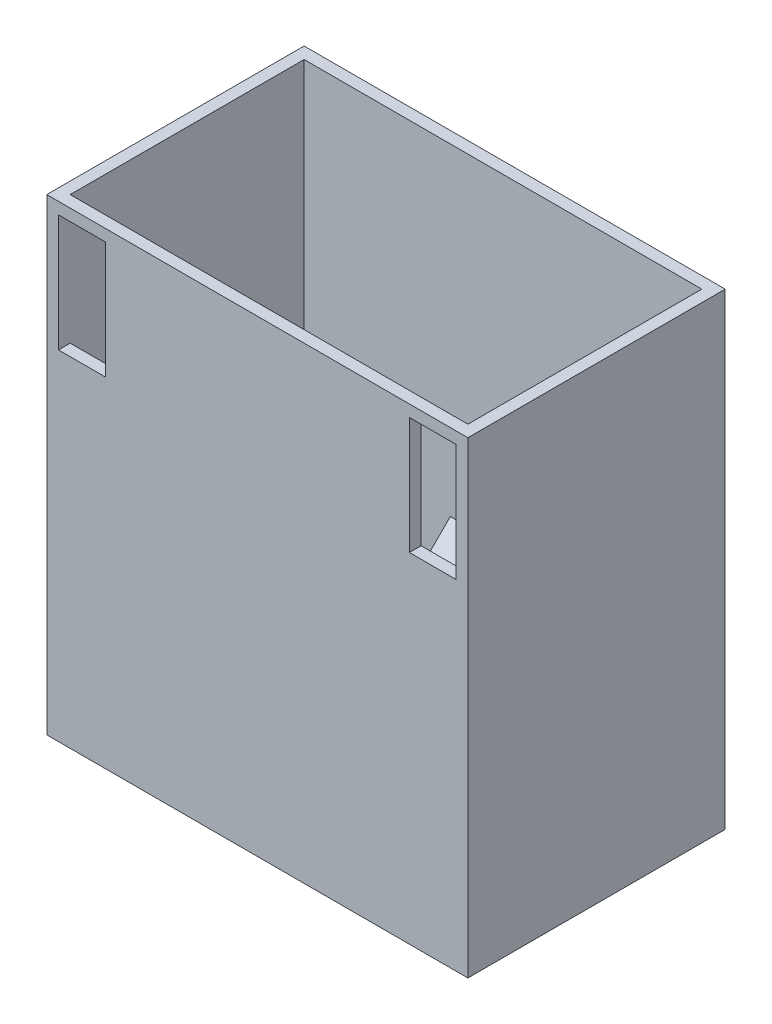
SolidWorks part; units mm, degrees
ref_plane "Front Plane" through (0, 0, 0) normal (0, 0, 1) x (1, 0, 0)
ref_plane "Top Plane" through (0, 0, 0) normal (0, 1, 0) x (1, 0, 0)
ref_plane "Right Plane" through (0, 0, 0) normal (1, 0, 0) x (0, 0, -1)
sketch "Sketch2" plane through (0, 0, 0) normal (0, 1, 0) x (1, 0, 0)
  line L1 (0, 0) -> (90, 0)
  line L2 (0, 0) -> (0, 55)
  line L3 (0, 55) -> (90, 55)
  line L4 (90, 0) -> (90, 55)
  dimension "D1" = 90
  dimension "D2" = 55
extrude "Boss-Extrude1" add sketch "Sketch2" along normal blind 100
sketch "Sketch3" plane through (0, 100, 0) normal (0, 1, 0) x (1, 0, 0)
  line L0 (2.5, 2.5) -> (2.5, 0) construction
  line L1 (2.5, 2.5) -> (87.5, 2.5)
  line L2 (2.5, 2.5) -> (2.5, 52.5)
  line L3 (2.5, 52.5) -> (87.5, 52.5)
  line L4 (87.5, 2.5) -> (87.5, 52.5)
  line L5 (0, 0) -> (90, 0) construction
  line L6 (2.5, 0) -> (2.5, 2.5) construction
  line L7 (0, 2.5) -> (2.5, 2.5) construction
  line L8 (0, 55) -> (0, 0) construction
  line L9 (87.5, 52.5) -> (87.5, 55) construction
  line L10 (90, 55) -> (0, 55) construction
  line L11 (87.5, 2.5) -> (90, 2.5) construction
  line L12 (90, 0) -> (90, 55) construction
  dimension "D1" = 2.5
extrude "Cut-Extrude1" cut sketch "Sketch3" against normal blind 95
ref_plane "Plane2" through (36.25, 0, 0) normal (1, 0, 0) x (0, 0, -1)
sketch "Sketch4" plane through (0, 0, 0) normal (0, -1, 0) x (1, 0, 0)
  line L0 (45, -55) -> (45, 0) construction
  line L1 (90, -55) -> (0, -55) construction
  line L2 (0, 0) -> (90, 0) construction
  line L4 (36.25, -25) -> (53.75, -25)
  line L5 (36.25, -25) -> (36.25, -55)
  line L6 (36.25, -55) -> (53.75, -55)
  line L7 (53.75, -25) -> (53.75, -55)
  line L8 (36.25, -25) -> (53.75, -55) construction
  line L9 (36.25, -55) -> (53.75, -25) construction
  point P6 (45, -40)
  dimension "D1" = 25
  dimension "D2" = 17.5
sketch "Sketch5" plane through (0, 0, -55) normal (0, 0, -1) x (-1, 0, 0)
  line L0 (-53.75, 0) -> (-53.75, 30) construction
  line L1 (-36.25, 0) -> (-53.75, 0) construction
  line L2 (-53.75, 30) -> (-36.25, 30)
  line L3 (-36.25, 0) -> (-36.25, 30) construction
  line L4 (-36.25, 0) -> (-53.75, 0) construction
  line L5 (-36.25, 0) -> (-53.75, 0) construction
  line L6 (-90, 0) -> (0, 0) construction
  line L7 (-90, 0) -> (0, 0) construction
  line L8 (-45, 0) -> (-45, 100) construction
  line L9 (-90, 100) -> (0, 100) construction
  point P19 (-21.9555, 30)
  point P20 (-45, 30)
  dimension "D1" = 30
  dimension "D2" = 17.5
sketch "Sketch6" plane through (0, 0, -52.5) normal (0, 0, 1) x (1, 0, 0)
  line L0 (36.25, 30) -> (53.75, 30)
ref_plane "Plane1" through (0, 30, 0) normal (0, -1, 0) x (-1, 0, 0)
sketch "Sketch10" plane through (36.25, 0, 0) normal (1, 0, 0) x (0, 0, -1)
  line L0 (55, 30) -> (55, 0)
  line L3 (55, 0) -> (25, 0)
  line L6 (25, 0) -> (21.4645, 0)
  line L7 (55, 0) -> (0, 0) construction
  line L8 (21.4645, 0) -> (55, 33.5355)
  line L9 (55, 100) -> (55, 0) construction
  line L10 (55, 33.5355) -> (55, 30)
  dimension "D1" = 2.5
  dimension "D2" = 2.5
  dimension "D3" = 30
  dimension "D4" = 30
extrude "Boss-Extrude4" add sketch "Sketch10" along normal blind 20 and the other way blind 2.5
sketch "Sketch7" plane through (0, 30, 0) normal (0, -1, 0) x (-1, 0, 0)
  line L0 (-36.25, 25) -> (-36.25, 55) construction
  line L1 (-53.75, 55) -> (-36.25, 55)
  line L2 (-53.75, 55) -> (-53.75, 52.5)
  line L3 (-53.75, 52.5) -> (-36.25, 52.5)
  line L4 (-36.25, 55) -> (-36.25, 52.5)
  line L5 (-36.25, 52.5) -> (-53.75, 52.5) construction
loft "Cut-Loft4" cut profiles "Sketch4", "Sketch7"
sketch "Sketch11" plane through (0, 0, 0) normal (0, 0, 1) x (1, 0, 0)
  line L0 (0, 100) -> (90, 100) construction
  line L1 (87.5, 97.5) -> (77.5, 97.5)
  line L2 (87.5, 97.5) -> (87.5, 72.5)
  line L3 (87.5, 72.5) -> (77.5, 72.5)
  line L4 (77.5, 97.5) -> (77.5, 72.5)
  line L5 (45, 0) -> (45, 100) construction
  line L6 (0, 0) -> (90, 0) construction
  line L7 (90, 100) -> (90, 0) construction
  line L8 (2.5, 72.5) -> (12.5, 72.5)
  line L9 (12.5, 97.5) -> (12.5, 72.5)
  line L10 (2.5, 97.5) -> (12.5, 97.5)
  line L11 (2.5, 97.5) -> (2.5, 72.5)
  dimension "D1" = 2.5
  dimension "D2" = 10
  dimension "D3" = 25
  dimension "D4" = 2.5
extrude "Cut-Extrude2" cut sketch "Sketch11" against normal up to next
